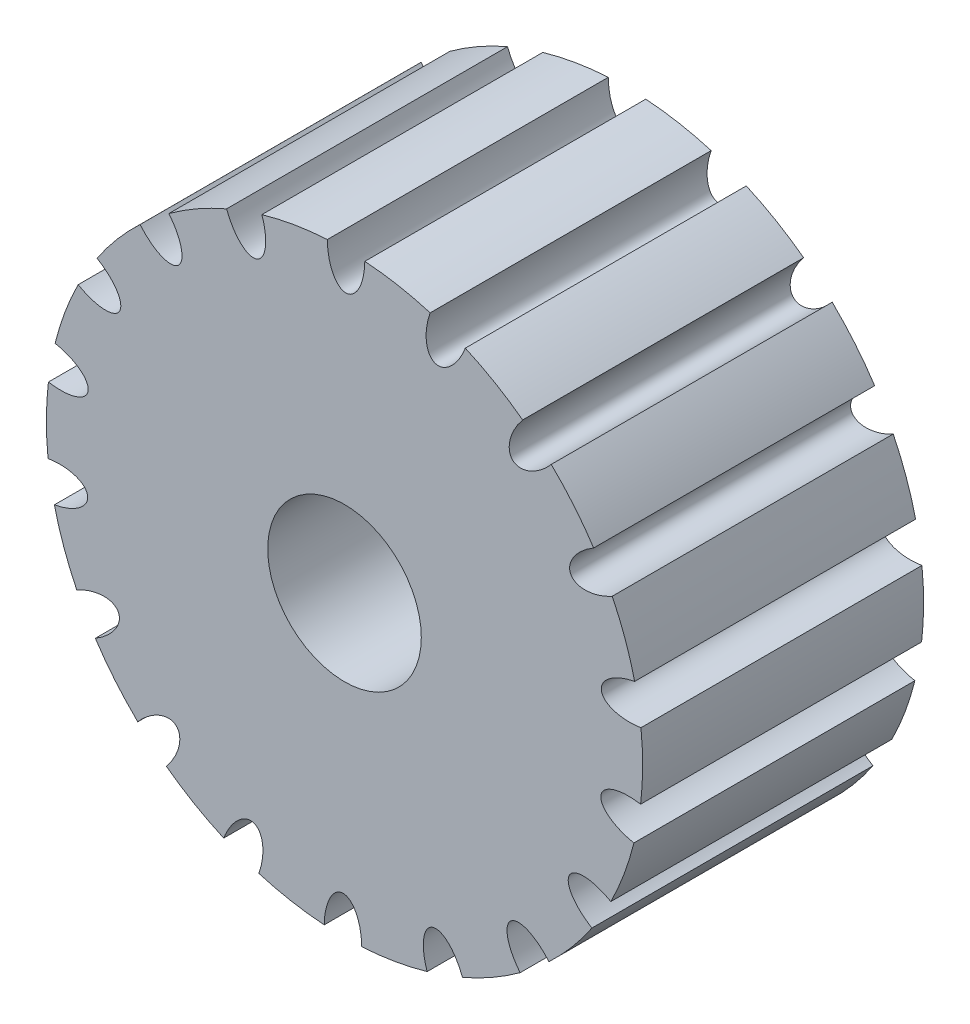
SolidWorks part; units mm, degrees
ref_plane "Front" through (0, 0, 0) normal (0, 0, 1) x (1, 0, 0)
ref_plane "Top" through (0, 0, 0) normal (0, 1, 0) x (1, 0, 0)
ref_plane "Right" through (0, 0, 0) normal (1, 0, 0) x (0, 0, -1)
sketch "Эскиз1" plane through (0, 0, 0) normal (0, 0, 1) x (1, 0, 0)
  circle A0 centre (0, 0) radius 15.9155
  dimension "D1" = 31.831
extrude "Бобышка-Вытянуть1" add sketch "Эскиз1" along normal blind 15
sketch "Эскиз2" plane through (0, 0, 15) normal (0, 0, 1) x (1, 0, 0)
  circle A0 centre (0, 0) radius 4.1
  dimension "D1" = 8.2
extrude "Вырез-Вытянуть5" cut sketch "Эскиз2" against normal blind 15
sketch "Эскиз5" plane through (0, 0, 15) normal (0, 0, 1) x (1, 0, 0)
  circle A0 centre (0, 0) radius 15.9155 construction
  ellipse E0 centre (0.0828, 15.9153) end of major axis (0.0932, 17.9153) minor radius 1
extrude "Вырез-Вытянуть6" cut sketch "Эскиз5" against normal blind 15
pattern_circular "Круговой массив2" count 18 over 360 about axis through (0, 0, 0) along (0, 0, 1) of "Вырез-Вытянуть6"
